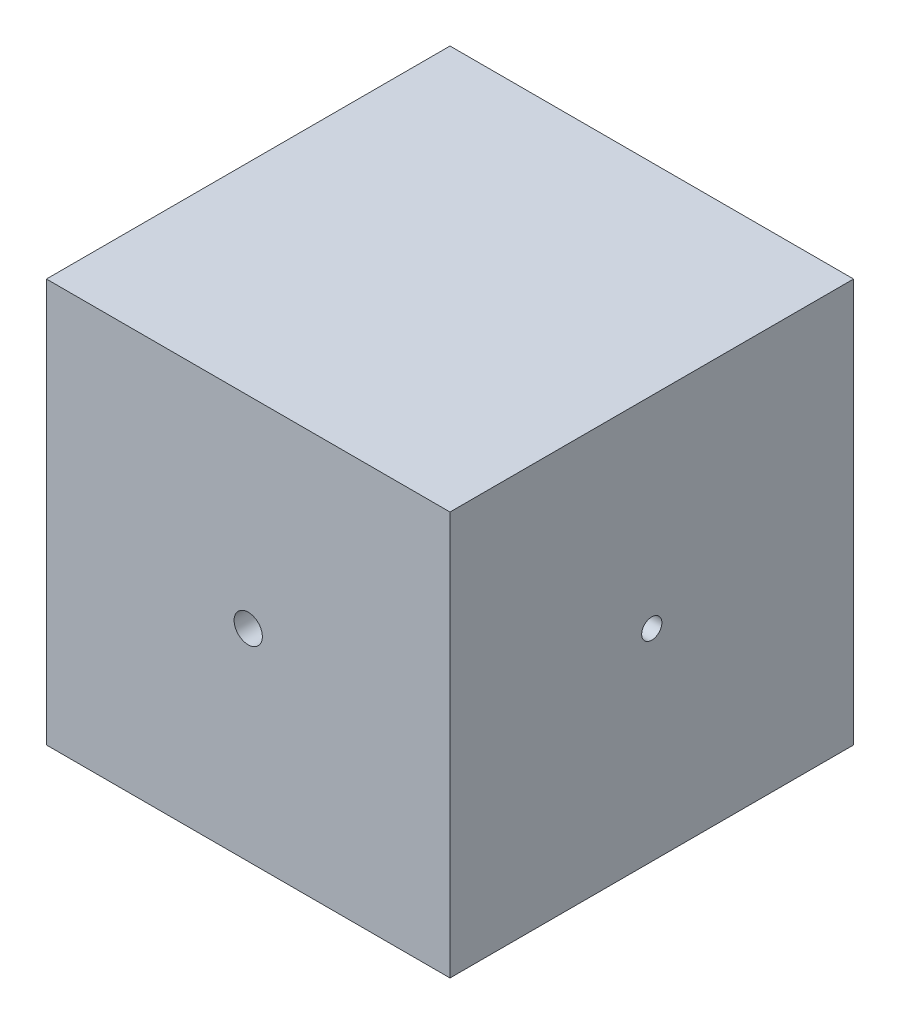
SolidWorks part; units mm, degrees
ref_plane "Front Plane" through (0, 0, 0) normal (0, 0, 1) x (1, 0, 0)
ref_plane "Top Plane" through (0, 0, 0) normal (0, 1, 0) x (1, 0, 0)
ref_plane "Right Plane" through (0, 0, 0) normal (1, 0, 0) x (0, 0, -1)
sketch "Sketch1" plane through (0, 0, 0) normal (0, 0, 1) x (1, 0, 0)
  line L1 (-50, 50) -> (50, 50)
  line L2 (-50, 50) -> (-50, -50)
  line L3 (-50, -50) -> (50, -50)
  line L4 (50, 50) -> (50, -50)
  line L5 (-50, 50) -> (50, -50) construction
  line L6 (-50, -50) -> (50, 50) construction
  point P0 (0, 0)
  dimension "D1" = 100
extrude "Boss-Extrude1" add sketch "Sketch1" along normal mid plane 100
hole_wizard "M8x1.25 Tapped Hole1" positions "Sketch2" profile "Sketch3" tap size "M8x1.25" standard "ANSI Metric"
sketch "Sketch2" plane through (-50, 0, 0) normal (-1, 0, 0) x (0, 0, 1)
  point P0 (0, 0)
cosmetic thread "Hole Thread1" parameters "D2"=8
sketch "Sketch3" plane through (-50, 0, 0) normal (0, 1, 0) x (0, 0, 1)
  line L0 (0, 0) -> (0, 29.7929)
  line L1 (0, 29.7929) -> (3.4, 27.75)
  line L2 (3.4, 27.75) -> (3.4, 0)
  line L5 (3.4, 0) -> (0, 0)
  line L10 (0, 29.7929) -> (-3.4, 27.75) construction
  line L11 (0, -6.35) -> (0, 107.95) construction
  dimension "Tap Drill Dia." = 6.8
  dimension "Tap Drill Depth" = 27.75
  dimension "Drill Angle" = 118
hole_wizard "M8x1.0 Tapped Hole1" positions "Sketch4" profile "Sketch5" tap size "M8x1.0" standard "ANSI Metric"
sketch "Sketch4" plane through (0, 0, 50) normal (0, 0, 1) x (1, 0, 0)
  point P0 (0, 0)
sketch "Sketch5" plane through (0, 0, 50) normal (1, 0, 0) x (0, -1, 0)
  line L0 (0, 0) -> (0, 21.103)
  line L1 (0, 21.103) -> (3.5, 19)
  line L2 (3.5, 19) -> (3.5, 0)
  line L5 (3.5, 0) -> (0, 0)
  line L10 (0, 21.103) -> (-3.5, 19) construction
  line L11 (0, -6.35) -> (0, 107.95) construction
  dimension "Tap Drill Dia." = 7
  dimension "Tap Drill Depth" = 19
  dimension "Drill Angle" = 118
cosmetic thread "Hole Thread2" parameters "D1"=16, "D2"=8
hole_wizard "M6x1.0 Tapped Hole1" positions "Sketch6" profile "Sketch7" tap size "M6x1.0" standard "ANSI Metric"
sketch "Sketch6" plane through (50, 0, 0) normal (1, 0, 0) x (0, 0, -1)
  point P0 (0, 0)
sketch "Sketch7" plane through (50, 0, 0) normal (0, 1, 0) x (0, 0, -1)
  line L0 (0, 0) -> (0, 16.5022)
  line L1 (0, 16.5022) -> (2.5, 15)
  line L2 (2.5, 15) -> (2.5, 0)
  line L5 (2.5, 0) -> (0, 0)
  line L10 (0, 16.5022) -> (-2.5, 15) construction
  line L11 (0, -6.35) -> (0, 107.95) construction
  dimension "Tap Drill Dia." = 5
  dimension "Tap Drill Depth" = 15
  dimension "Drill Angle" = 118
cosmetic thread "Hole Thread3" parameters "D1"=12, "D2"=6
hole_wizard "CBORE for M12 SHCS1" positions "Sketch8" profile "Sketch9" counterbore size "M12" standard "ANSI Metric"
sketch "Sketch8" plane through (0, 0, -50) normal (0, 0, -1) x (-1, 0, 0)
  point P0 (0, 0)
sketch "Sketch9" plane through (0, 0, -50) normal (1, 0, 0) x (0, 1, 0)
  line L0 (0, 0) -> (0, 39.0558)
  line L1 (0, 39.0558) -> (6.75, 35)
  line L2 (6.75, 35) -> (6.75, 12)
  line L3 (6.75, 12) -> (10, 12)
  line L4 (10, 12) -> (10, 0)
  line L5 (10, 0) -> (0, 0)
  line L10 (0, 39.0558) -> (-6.75, 35) construction
  line L11 (0, -6.35) -> (0, 107.95) construction
  dimension "Hole Dia." = 13.5
  dimension "Hole Depth" = 35
  dimension "C'Bore Dia." = 20
  dimension "C'Bore Depth" = 12
  dimension "Drill Angle" = 118
